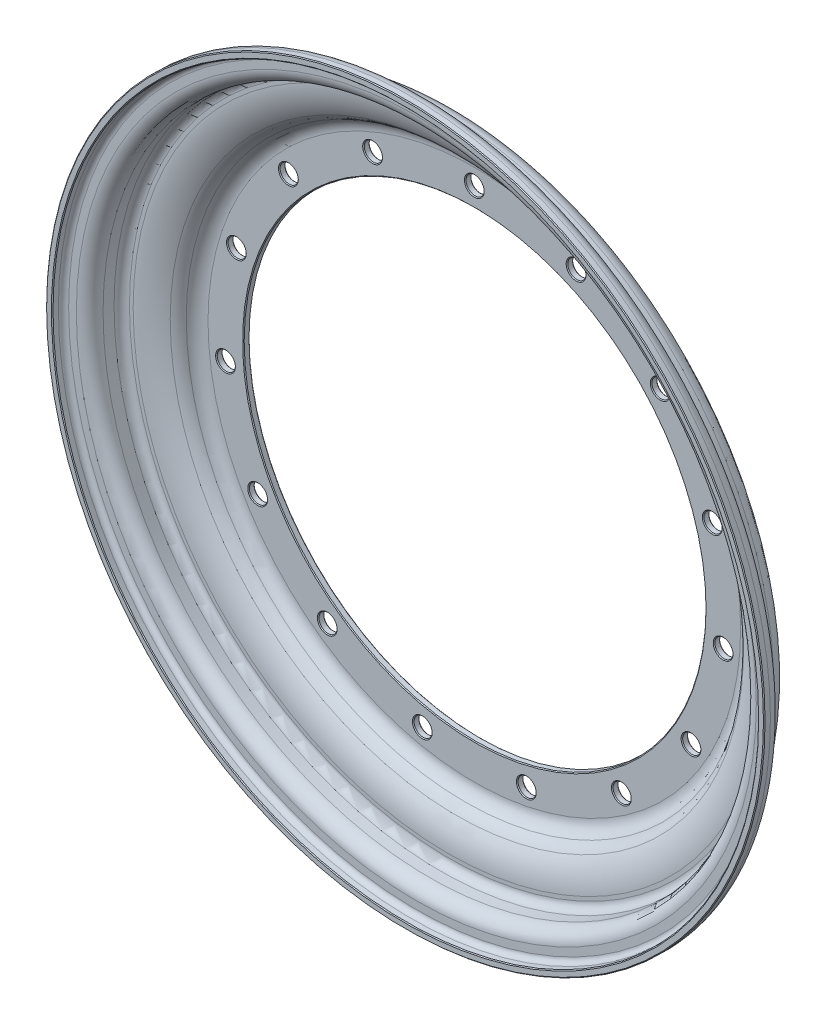
SolidWorks part; units mm, degrees
material "6061-T6 (SS)"
ref_plane "Front Plane" through (0, 0, 0) normal (0, 0, 1) x (1, 0, 0)
ref_plane "Top Plane" through (0, 0, 0) normal (0, 1, 0) x (1, 0, 0)
ref_plane "Right Plane" through (0, 0, 0) normal (1, 0, 0) x (0, 0, -1)
ref_axis "Axis1" through (0, 0, -1.8731) along (0, 0, 1)
sketch "Sketch1" plane through (0, 0, 0) normal (1, 0, 0) x (0, 0, -1)
  line L0 (0, 114.3) -> (0, 131.8108)
  line L1 (-12.8246, 156.0362) -> (-12.8246, 157.8624)
  line L2 (-19.8095, 164.8473) -> (-25.2705, 164.8473)
  line L3 (-28.6991, 168.2759) -> (-28.6991, 172.0859)
  line L4 (-34.4142, 177.801) -> (-37.4622, 177.801)
  line L5 (-3.175, 114.3) -> (-3.175, 131.8108)
  line L6 (-15.9996, 156.0362) -> (-15.9996, 157.8624)
  line L7 (-19.8095, 161.6723) -> (-25.2705, 161.6723)
  line L8 (-31.8741, 168.2759) -> (-31.8741, 172.0859)
  line L9 (-34.4142, 174.626) -> (-37.4622, 174.626)
  line L10 (-37.4622, 177.801) -> (-37.4622, 174.626)
  line L11 (-3.175, 114.3) -> (0, 114.3)
  arc A0 (0, 131.8108) -> (-6.2586, 141.1935) centre (-10.1625, 131.8108) ccw
  arc A1 (-6.2586, 141.1935) -> (-9.1491, 143.604) centre (-3.8185, 147.0578) cw
  arc A2 (-9.1491, 143.604) -> (-12.8246, 156.0362) centre (10.0384, 156.0362) cw
  arc A3 (-12.8246, 157.8624) -> (-19.8095, 164.8473) centre (-19.8095, 157.8624) ccw
  arc A4 (-25.2705, 164.8473) -> (-28.6991, 168.2759) centre (-25.2705, 168.2759) cw
  arc A5 (-28.6991, 172.0859) -> (-34.4142, 177.801) centre (-34.4142, 172.0859) ccw
  arc A6 (-3.175, 131.8108) -> (-7.4782, 138.2621) centre (-10.1625, 131.8108) ccw
  arc A7 (-7.4782, 138.2621) -> (-11.8137, 141.8775) centre (-3.8185, 147.0578) cw
  arc A8 (-11.8137, 141.8775) -> (-15.9996, 156.0362) centre (10.0384, 156.0362) cw
  arc A9 (-15.9996, 157.8624) -> (-19.8095, 161.6723) centre (-19.8095, 157.8624) ccw
  arc A10 (-25.2705, 161.6723) -> (-31.8741, 168.2759) centre (-25.2705, 168.2759) cw
  arc A11 (-31.8741, 172.0859) -> (-34.4142, 174.626) centre (-34.4142, 172.0859) ccw
  dimension "D1" = 114.3
  dimension "D2" = 17.5108
  dimension "D3" = 9.3828
  dimension "D4" = 2.8905
  dimension "D5" = 6.2586
  dimension "D6" = 2.4105
  dimension "D7" = 1.8263
  dimension "D8" = 12.9642
  dimension "D9" = 9.8781
  dimension "D10" = 5.461
  dimension "D11" = 4.8489
  dimension "D12" = 3.81
  dimension "D13" = 8.0823
  dimension "D14" = 3.048
  dimension "D15" = 3.175
revolve "Inner Rim" add sketch "Sketch1" angle 360 about axis through (0, 0, -1.8731) along (0, 0, 1)
sketch "Sketch2" plane through (0, 0, 3.175) normal (0, 0, 1) x (1, 0, 0)
  circle A0 centre (0, 123.825) radius 4.4983
  circle A1 centre (0, 0) radius 114.3 construction
  dimension "D2" = 8.9967
  dimension "D1" = 9.525
extrude "Mounting Hole" cut sketch "Sketch2" against normal through all
pattern_circular "Mounting Hole Pattern" count 15 over 360 about axis through (0, 0, 0) along (0, 0, 1) of "Mounting Hole"
chamfer "Edge Chamfer" distance 0.3962 angle 45 34 edges at (-114.3, 0, 0) (4.4983, 123.825, 0) (-46.2547, 114.9494, 0) (-89.0099, 86.198, 0) (-116.3745, 42.5422, 0) (-123.6169, -8.4695, 0) (-109.4848, -58.0168, 0) (-76.4217, -97.5325, 0) (-30.1447, -120.1839, 0) (21.3446, -122.0544, 0) (69.1433, -102.8206, 0) (104.9864, -65.8082, 0) (122.6765, -17.4169, 0) (119.1546, 33.9859, 0) (95.0299, 79.5122, 0) (54.4736, 111.2901, 0) (-114.3, 0, 3.175) (4.4983, 123.825, 3.175) (-46.2547, 114.9494, 3.175) (-89.0099, 86.198, 3.175) (-116.3745, 42.5422, 3.175) (-123.6169, -8.4695, 3.175) (-109.4848, -58.0168, 3.175) (-76.4217, -97.5325, 3.175) (-30.1447, -120.1839, 3.175) (21.3446, -122.0544, 3.175) (69.1433, -102.8206, 3.175) (104.9864, -65.8082, 3.175) (122.6765, -17.4169, 3.175) (119.1546, 33.9859, 3.175) (95.0299, 79.5122, 3.175) (54.4736, 111.2901, 3.175) (-177.801, 0, 37.4622) (-174.626, 0, 37.4622)
